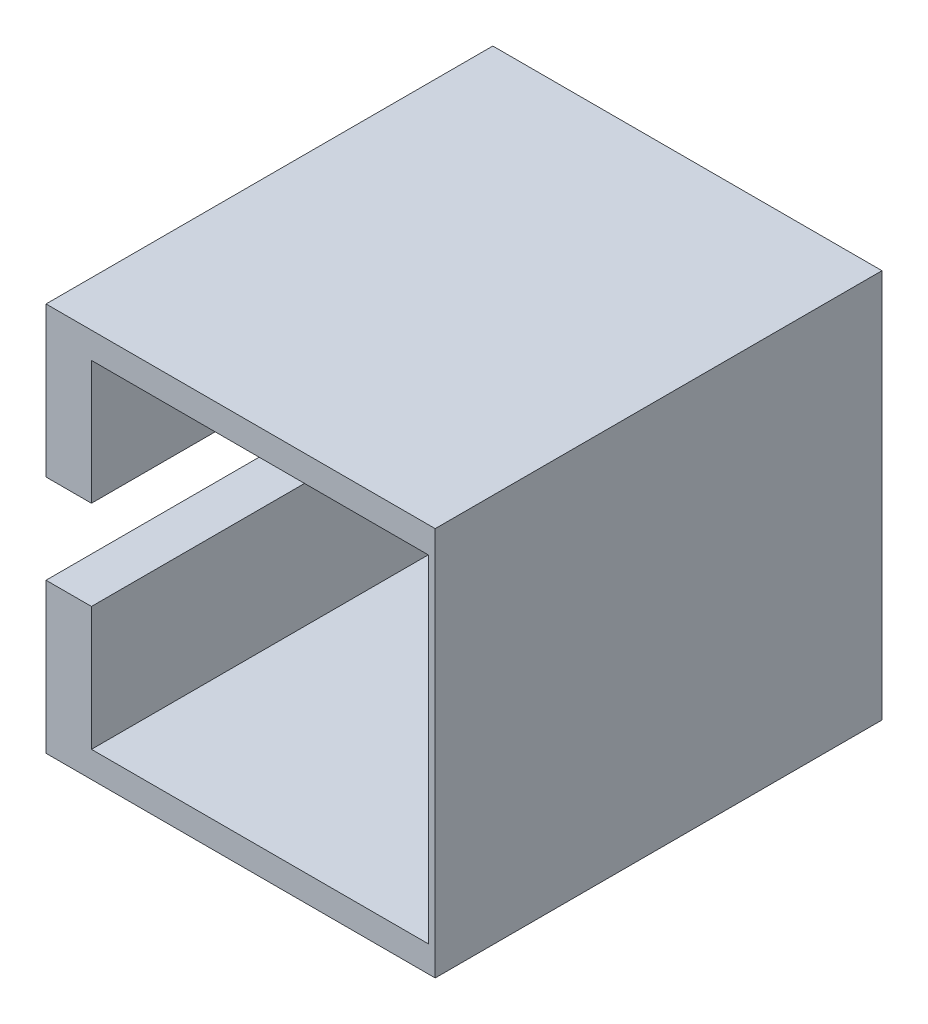
SolidWorks part; units mm, degrees
ref_plane "Front Plane" through (0, 0, 0) normal (0, 0, 1) x (1, 0, 0)
ref_plane "Top Plane" through (0, 0, 0) normal (0, 1, 0) x (1, 0, 0)
ref_plane "Right Plane" through (0, 0, 0) normal (1, 0, 0) x (0, 0, -1)
sketch "Sketch1" plane through (0, 0, 0) normal (0, 0, 1) x (1, 0, 0)
  line L1 (-13.3407, 10.0796) -> (8.7843, 10.0796)
  line L2 (-13.3407, 10.0796) -> (-13.3407, -12.0454)
  line L3 (-13.3407, -12.0454) -> (8.7843, -12.0454)
  line L4 (8.7843, 10.0796) -> (8.7843, -12.0454)
  line L5 (-13.3407, 10.0796) -> (8.7843, -12.0454) construction
  line L6 (-13.3407, -12.0454) -> (8.7843, 10.0796) construction
  line L7 (-10.7579, 8.5921) -> (8.3921, 8.5921)
  line L8 (-10.7579, 8.5921) -> (-10.7579, -10.5579)
  line L9 (-10.7579, -10.5579) -> (8.3921, -10.5579)
  line L10 (8.3921, 8.5921) -> (8.3921, -10.5579)
  line L11 (-10.7579, 8.5921) -> (8.3921, -10.5579) construction
  line L12 (-10.7579, -10.5579) -> (8.3921, 8.5921) construction
  line L13 (-10.7079, -10.5079) -> (8.3421, -10.5079) construction
  line L14 (-10.7079, -10.5079) -> (-10.7079, 8.5421) construction
  line L15 (-10.7079, 8.5421) -> (8.3421, 8.5421) construction
  line L16 (8.3421, -10.5079) -> (8.3421, 8.5421) construction
  line L17 (-10.7079, -10.5079) -> (8.3421, 8.5421) construction
  line L18 (-10.7079, 8.5421) -> (8.3421, -10.5079) construction
  point P0 (-2.2782, -0.9829)
  point P6 (-1.1329, -0.9329)
  point P11 (-1.1829, -0.9829)
  dimension "D2" = 19.15
  dimension "D3" = 1.4875
  dimension "D4" = 2.5829
  dimension "D5" = 0.3921
  dimension "D6" = 19.05
  dimension "D1" = 1.4875
extrude "Boss-Extrude1" add sketch "Sketch1" along normal mid plane 25.4
sketch "Sketch2" plane through (-13.3407, 0, 0) normal (-1, 0, 0) x (0, 0, 1)
  line L1 (0, -12.0454) -> (0, 10.0796) construction
  line L2 (12.7, -12.0454) -> (-12.7, -12.0454) construction
  line L3 (12.7, 10.0796) -> (-12.7, 10.0796) construction
  line L4 (-3.175, 1.5571) -> (12.7, 1.5571)
  line L5 (12.7, 10.0796) -> (12.7, -12.0454) construction
  line L6 (12.7, 1.5571) -> (12.7, -3.5229)
  line L7 (12.7, -3.5229) -> (-3.175, -3.5229)
  line L8 (-12.7, 10.0796) -> (-12.7, -12.0454) construction
  arc A1 (-3.175, 1.5571) -> (-3.175, -3.5229) centre (-3.175, -0.9829) ccw
  point P10 (0, -0.9829)
  dimension "D1" = 2.54
  dimension "D2" = 9.525
extrude "Cut-Extrude1" cut sketch "Sketch2" against normal blind 12.7
equation "\"D1@Sketch1\"=\"D3@Sketch1\""
